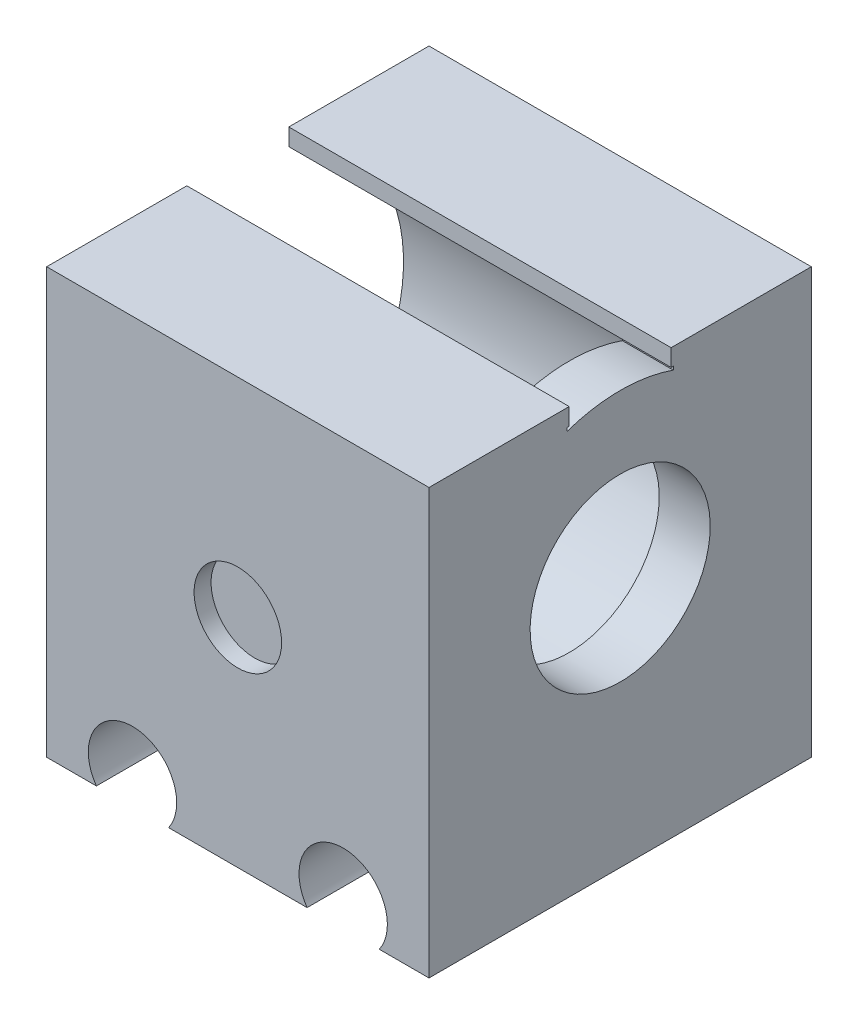
SolidWorks part; units mm, degrees
ref_plane "Front Plane" through (0, 0, 0) normal (0, 0, 1) x (1, 0, 0)
ref_plane "Top Plane" through (0, 0, 0) normal (0, 1, 0) x (1, 0, 0)
ref_plane "Right Plane" through (0, 0, 0) normal (1, 0, 0) x (0, 0, -1)
sketch "Sketch1" plane through (0, 0, 0) normal (0, 0, 1) x (1, 0, 0)
  line L1 (-14.2634, 22.0982) -> (30.7366, 22.0982)
  line L2 (-14.2634, 22.0982) -> (-14.2634, -27.9018)
  line L3 (-14.2634, -27.9018) -> (30.7366, -27.9018)
  line L4 (30.7366, 22.0982) -> (30.7366, -27.9018)
  dimension "D1" = 50
  dimension "D2" = 45
extrude "Boss-Extrude1" add sketch "Sketch1" along normal blind 45
sketch "Sketch2" plane through (0, 0, 45) normal (0, 0, 1) x (1, 0, 0)
  line L0 (-14.2634, -27.9018) -> (30.7366, -27.9018) construction
  line L1 (-14.2634, 22.0982) -> (-14.2634, -27.9018) construction
  circle A0 centre (-4.1634, -24.9018) radius 5.2
  circle A1 centre (20.6366, -24.9018) radius 5.2
  dimension "D1" = 3
  dimension "D3" = 10.1
  dimension "D2" = 2
extrude "Cut-Extrude1" cut sketch "Sketch2" against normal blind 45
sketch "Sketch3" plane through (30.7366, 0, 0) normal (1, 0, 0) x (0, 0, -1)
  line L0 (-22.5, 22.0982) -> (-22.5, -1.4211) construction
  line L1 (-45, 22.0982) -> (0, 22.0982) construction
  circle A0 centre (-22.5, 1.6132) radius 19.125
extrude "Cut-Extrude2" cut sketch "Sketch3" against normal blind 45
sketch "Sketch4" plane through (30.7366, 0, 0) normal (1, 0, 0) x (0, 0, -1)
  line L1 (-28.75, 23.3717) -> (-16.25, 23.3717)
  line L2 (-28.75, 23.3717) -> (-28.75, 18.5203)
  line L3 (-28.75, 18.5203) -> (-16.25, 18.5203)
  line L4 (-16.25, 23.3717) -> (-16.25, 18.5203)
  line L6 (-45, -27.9018) -> (-45, 22.0982) construction
  dimension "D1" = 12.5
  dimension "D2" = 16.25
extrude "Cut-Extrude3" cut sketch "Sketch4" against normal blind 45
sketch "Sketch5" plane through (30.7366, 0, 0) normal (1, 0, 0) x (0, 0, -1)
  line L0 (-41.625, 1.6132) -> (-3.375, 1.6132) construction
  arc A0 (-28.75, 19.6881) -> (-16.25, 19.6881) centre (-22.5, 1.6132) ccw construction
  circle A1 centre (-22.5, 1.6132) radius 19.125
extrude "Boss-Extrude2" add sketch "Sketch5" against normal blind 6
sketch "Sketch6" plane through (30.7366, 0, 0) normal (1, 0, 0) x (0, 0, -1)
  line L0 (-41.625, 1.6132) -> (-3.375, 1.6132) construction
  circle A0 centre (-22.5, 1.6132) radius 10.6
extrude "Cut-Extrude4" cut sketch "Sketch6" against normal blind 6
sketch "Sketch7" plane through (-14.2634, 0, 0) normal (-1, 0, 0) x (0, 0, 1)
  line L0 (3.375, 1.6132) -> (22.5, 1.6132) construction
  arc A0 (16.25, 19.6881) -> (28.75, 19.6881) centre (22.5, 1.6132) ccw construction
  arc A1 (16.25, 19.6881) -> (28.75, 19.6881) centre (22.5, 1.6132) ccw construction
  circle A2 centre (22.5, 1.6132) radius 19.5
extrude "Cut-Extrude5" cut sketch "Sketch7" against normal blind 39
sketch "Sketch8" plane through (-14.2634, 0, 0) normal (-1, 0, 0) x (0, 0, 1)
  line L0 (16.25, 20.0844) -> (16.25, 22.0982) construction
  line L7 (16.25, 20.0844) -> (16.5, 20.0844)
  line L8 (16.25, 20.0844) -> (16.25, 22.0982)
  line L9 (16.25, 22.0982) -> (16.5, 22.0982)
  line L10 (16.5, 20.0844) -> (16.5, 22.0982)
  line L11 (28.5, 22.0982) -> (28.75, 22.0982)
  line L12 (28.5, 22.0982) -> (28.5, 20.0844)
  line L13 (28.5, 20.0844) -> (28.75, 20.0844)
  line L14 (28.75, 22.0982) -> (28.75, 20.0844)
  dimension "D1" = 0.25
extrude "Boss-Extrude3" add sketch "Sketch8" against normal blind 45
sketch "Sketch9" plane through (0, 0, 45) normal (0, 0, 1) x (1, 0, 0)
  line L0 (8.2366, 22.0982) -> (8.2366, -2.4018) construction
  line L1 (30.7366, 22.0982) -> (-14.2634, 22.0982) construction
  circle A0 centre (8.2366, -2.4018) radius 5.15
  dimension "D1" = 24.5
extrude "Cut-Extrude6" cut sketch "Sketch9" against normal blind 2
sketch "Sketch10" plane through (0, 0, 0) normal (0, 0, -1) x (-1, 0, 0)
  line L0 (-8.2366, 22.0982) -> (-8.2366, -2.4018) construction
  line L1 (-30.7366, 22.0982) -> (14.2634, 22.0982) construction
  circle A0 centre (-8.2366, -2.4018) radius 5.15
  dimension "D1" = 24.5
extrude "Cut-Extrude7" cut sketch "Sketch10" against normal blind 2
